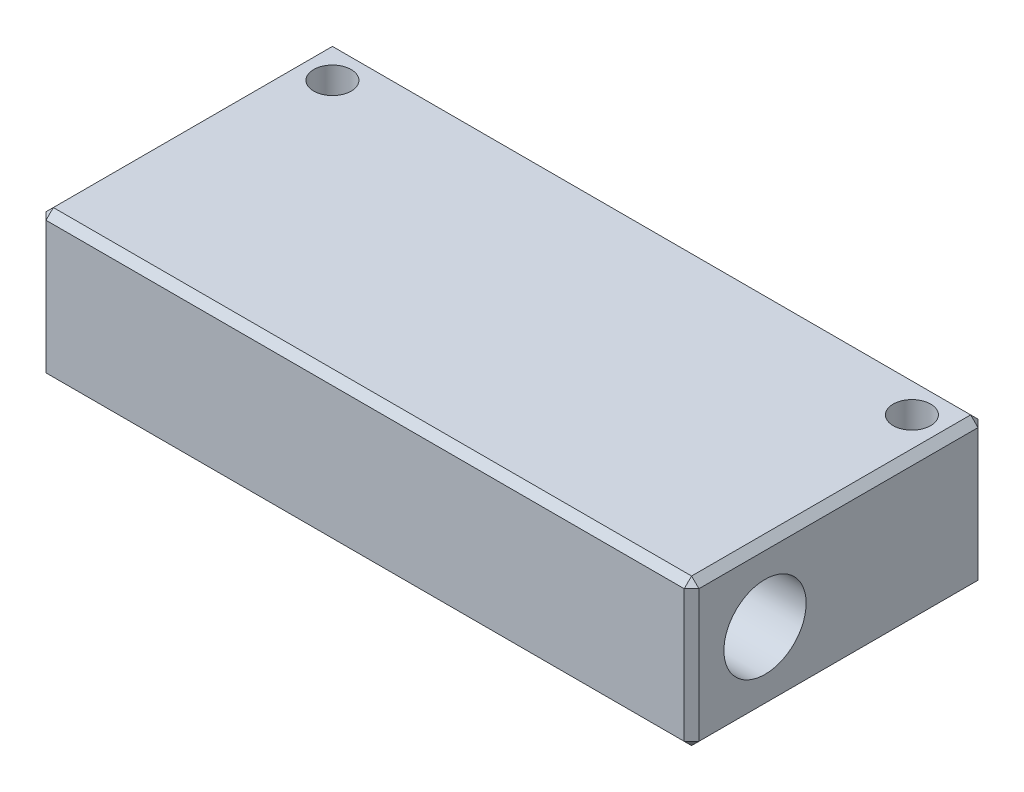
SolidWorks part; units mm, degrees
ref_plane "Front Plane" through (0, 0, 0) normal (0, 0, 1) x (1, 0, 0)
ref_plane "Top Plane" through (0, 0, 0) normal (0, 1, 0) x (1, 0, 0)
ref_plane "Right Plane" through (0, 0, 0) normal (1, 0, 0) x (0, 0, -1)
sketch "Sketch1" plane through (0, 0, 0) normal (0, 1, 0) x (1, 0, 0)
  line L1 (-44.45, -20) -> (44.45, -20)
  line L2 (-44.45, -20) -> (-44.45, 20)
  line L3 (-44.45, 20) -> (44.45, 20)
  line L4 (44.45, -20) -> (44.45, 20)
  line L5 (-44.45, -20) -> (44.45, 20) construction
  line L6 (-44.45, 20) -> (44.45, -20) construction
  point P0 (0, 0)
  dimension "D1" = 40
  dimension "D2" = 88.9
extrude "Boss-Extrude1" add sketch "Sketch1" along normal blind 20
sketch "Sketch2" plane through (44.45, 0, 0) normal (1, 0, 0) x (0, 0, -1)
  line L0 (-20, 20) -> (-20, 0) construction
  line L1 (-20, 0) -> (20, 0) construction
  circle A0 centre (-10, 10) radius 5
  dimension "D1" = 10
  dimension "D3" = 10
  dimension "D2" = 10
extrude "Cut-Extrude1" cut sketch "Sketch2" against normal through all
sketch "Sketch3" plane through (44.45, 0, 0) normal (1, 0, 0) x (0, 0, -1)
  circle A0 centre (-10, 10) radius 5.6
  dimension "D1" = 11.2
extrude "Cut-Extrude2" cut sketch "Sketch3" against normal blind 10
mirror "Mirror1" about plane through (0, 0, 0) normal (1, 0, 0) of "Cut-Extrude2"
sketch "Sketch4" plane through (0, 0, -20) normal (0, 0, -1) x (-1, 0, 0)
  line L0 (-44.45, 0) -> (44.45, 0) construction
  circle A0 centre (-22.5, 10) radius 4
  circle A1 centre (22.5, 10) radius 4
  point P4 (0, 0)
  dimension "D1" = 45
  dimension "D3" = 8
  dimension "D2" = 22.5
  dimension "D4" = 10
extrude "Cut-Extrude3" cut sketch "Sketch4" against normal blind 10
hole_wizard "1/4-20 Tapped Hole1" positions "Sketch6" profile "Sketch5" tap size "1/4-20" standard "ANSI Inch" end condition through all
sketch "Sketch6" plane through (0, 20, 0) normal (0, 1, 0) x (1, 0, 0)
  line L0 (44.45, -20) -> (44.45, 20) construction
  line L1 (44.45, 20) -> (-44.45, 20) construction
  line L2 (-44.45, 20) -> (-44.45, -20) construction
  point P0 (39.45, 15)
  point P2 (-39.45, 15)
  dimension "D1" = 5
  dimension "D2" = 5
  dimension "D3" = 5
  dimension "D4" = 5
sketch "Sketch5" plane through (39.45, 20, -15) normal (1, 0, 0) x (0, 0, 1)
  line L0 (0, 0) -> (0, 20)
  line L1 (0, 20) -> (2.5527, 20)
  line L2 (2.5527, 20) -> (2.5527, 0)
  line L5 (2.5527, 0) -> (0, 0)
  line L11 (0, -6.35) -> (0, 107.95) construction
  dimension "Thru Tap Drill Dia." = 5.1054
  dimension "Thru Tap Drill Depth" = 20
cosmetic thread "Hole Thread1" parameters "D2"=6.35
cosmetic thread "Hole Thread2" parameters "D2"=6.35
chamfer "Chamfer1" distance 1 angle 45 12 edges at (-44.45, 10, -20) (-44.45, 10, 20) (44.45, 10, 20) (0, 0, -20) (-44.45, 0, 0) (0, 0, 20) (44.45, 0, 0) (44.45, 10, -20) (-44.45, 20, 0) (0, 20, 20) (44.45, 20, 0) (0, 20, -20)
